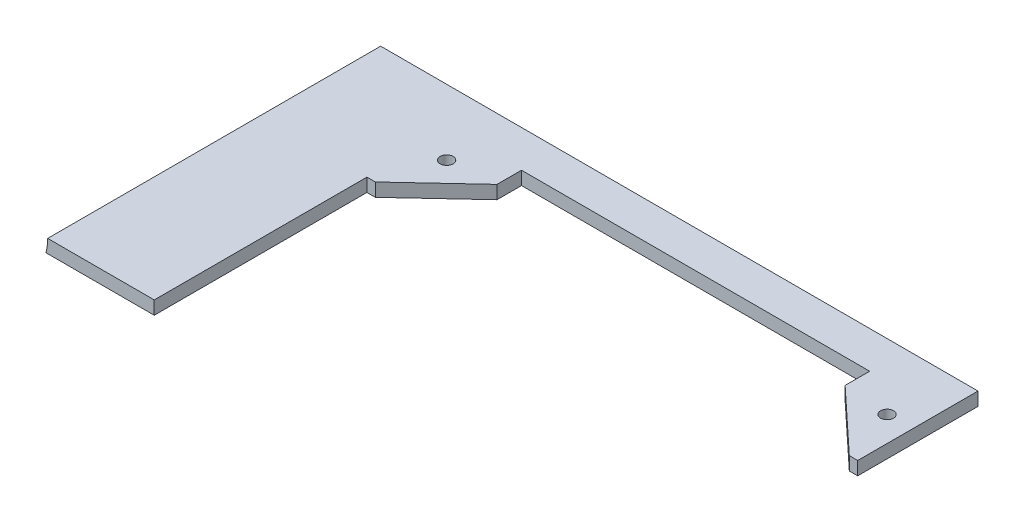
SolidWorks part; units mm, degrees
material "AISI 4130 Steel, annealed at 865C"
ref_plane "X-Y Datum" through (0, 0, 0) normal (0, 0, 1) x (1, 0, 0)
ref_plane "X-Z Datum" through (0, 0, 0) normal (0, 1, 0) x (1, 0, 0)
ref_plane "Y-Z Datum" through (0, 0, 0) normal (1, 0, 0) x (0, 0, -1)
sketch "Sketch1" plane through (0, 0, 0) normal (0, 1, 0) x (1, 0, 0)
  line L1 (-95.25, -38.1) -> (95.25, -38.1)
  line L2 (-95.25, -38.1) -> (-95.25, 38.1)
  line L3 (-95.25, 38.1) -> (95.25, 38.1)
  line L4 (95.25, -38.1) -> (95.25, 38.1)
  line L5 (-95.25, -38.1) -> (95.25, 38.1) construction
  line L6 (-95.25, 38.1) -> (95.25, -38.1) construction
  point P0 (0, 0)
  dimension "D1" = 190.5
  dimension "D2" = 76.2
extrude "Boss-Extrude1" add sketch "Sketch1" along normal blind 3.175 contours L3 L4 L1 L2
sketch "Sketch2" plane through (0, 3.175, 0) normal (0, 1, 0) x (1, 0, 0)
  line L0 (-56.5, 12.6) -> (-41.5, 26.6) construction
  line L1 (-41.5, 26.6) -> (-41.5, 32.45) construction
  line L2 (-41.5, 32.45) -> (41.5, 32.45) construction
  line L3 (41.5, 32.45) -> (41.5, 26.6) construction
  line L4 (-95.25, 38.1) -> (-95.25, -38.1)
  line L5 (-95.25, -38.1) -> (95.25, -38.1)
  line L6 (95.25, -38.1) -> (95.25, 38.1)
  line L7 (95.25, 38.1) -> (-95.25, 38.1)
  line L8 (-95.25, 38.1) -> (-95.25, -38.1)
  line L9 (-95.25, -38.1) -> (95.25, -38.1)
  line L10 (95.25, -38.1) -> (95.25, 38.1)
  line L11 (95.25, 38.1) -> (-95.25, 38.1)
  line L12 (41.5, 26.6) -> (56.5, 12.6) construction
  line L13 (-56.5, 12.6) -> (-41.5, 26.6)
  line L14 (-41.5, 26.6) -> (-41.5, 32.45)
  line L15 (-41.5, 32.45) -> (41.5, 32.45)
  line L16 (41.5, 32.45) -> (41.5, 26.6)
  line L17 (41.5, 26.6) -> (56.5, 12.6)
  line L18 (56.5, 12.6) -> (95.25, 12.6)
  line L19 (-56.5, 12.6) -> (-58.5, 12.6)
  line L20 (58.5, -451.9) -> (58.5, 38.1) construction
  line L21 (58.5, 12.6) -> (58.5, 38.1)
  line L22 (-58.5, 38.1) -> (-58.5, -451.9) construction
  line L23 (-58.5, 38.1) -> (-58.5, -38.1)
  circle A0 centre (-52.5052, 25.6052) radius 1.5453 construction
  circle A1 centre (52.5, 25.6052) radius 1.5453 construction
  circle A2 centre (-52.5052, 25.6052) radius 1.5453
  circle A3 centre (52.5, 25.6052) radius 1.5453
  line M6 (-95.25, -38.1) -> (95.25, -38.1)
  line M7 (95.25, -38.1) -> (95.25, 38.1)
  line M8 (95.25, 38.1) -> (-95.25, 38.1)
  dimension "D1" = 0
extrude "Cut-Extrude4" cut sketch "Sketch2" against normal through all contours L13 L19 L8 L18 L17 L16 L15 L14 M6 M7 | L21 L18 L10 M8 | A2 | A3
sketch "Sketch3" plane through (0, 0, -38.1) normal (0, 0, -1) x (-1, 0, 0)
  line L4 (95.25, 3.175) -> (-58.5, 3.175)
  line L5 (-58.5, 3.175) -> (-58.5, 0)
  line L6 (-58.5, 0) -> (95.25, 0)
  line L7 (95.25, 0) -> (95.25, 3.175)
  line L8 (95.25, 3.175) -> (-58.5, 3.175)
  line L9 (-58.5, 3.175) -> (-58.5, 0)
  line L10 (-58.5, 0) -> (95.25, 0)
  line L11 (95.25, 0) -> (95.25, 3.175)
  dimension "D1" = 0
extrude "Boss-Extrude2" add sketch "Sketch3" along normal blind 3.175
sketch "Sketch6" plane through (0, 0, 0) normal (0, -1, 0) x (1, 0, 0)
  line L0 (58.5, -41.275) -> (-95.25, -41.275) construction
  line L1 (58.5, -41.275) -> (-95.25, -41.275) construction
  line L14 (58.5, -38.1) -> (-95.25, -38.1) construction
  dimension "D1" = 3.175
sketch "Sketch7" plane through (0, 3.175, 0) normal (0, 1, 0) x (1, 0, 0)
  line L2 (-95.25, 38.1) -> (58.5, 38.1)
  line L3 (-95.25, 38.1) -> (58.5, 38.1) construction
  dimension "D1" = 3.175
sketch3d "3DSketch1"
  line L0 (-96.6, 3.175, 467.8839) -> (-96.6, 3.175, -36.6546)
  line L1 (-96.6, 3.175, -36.6546) -> (-96.6, 3.175, -207.1597)
sweep "Cut-Sweep1" cut path "3DSketch1" circular profile diameter 25.4 parameters "D3"=25.4
